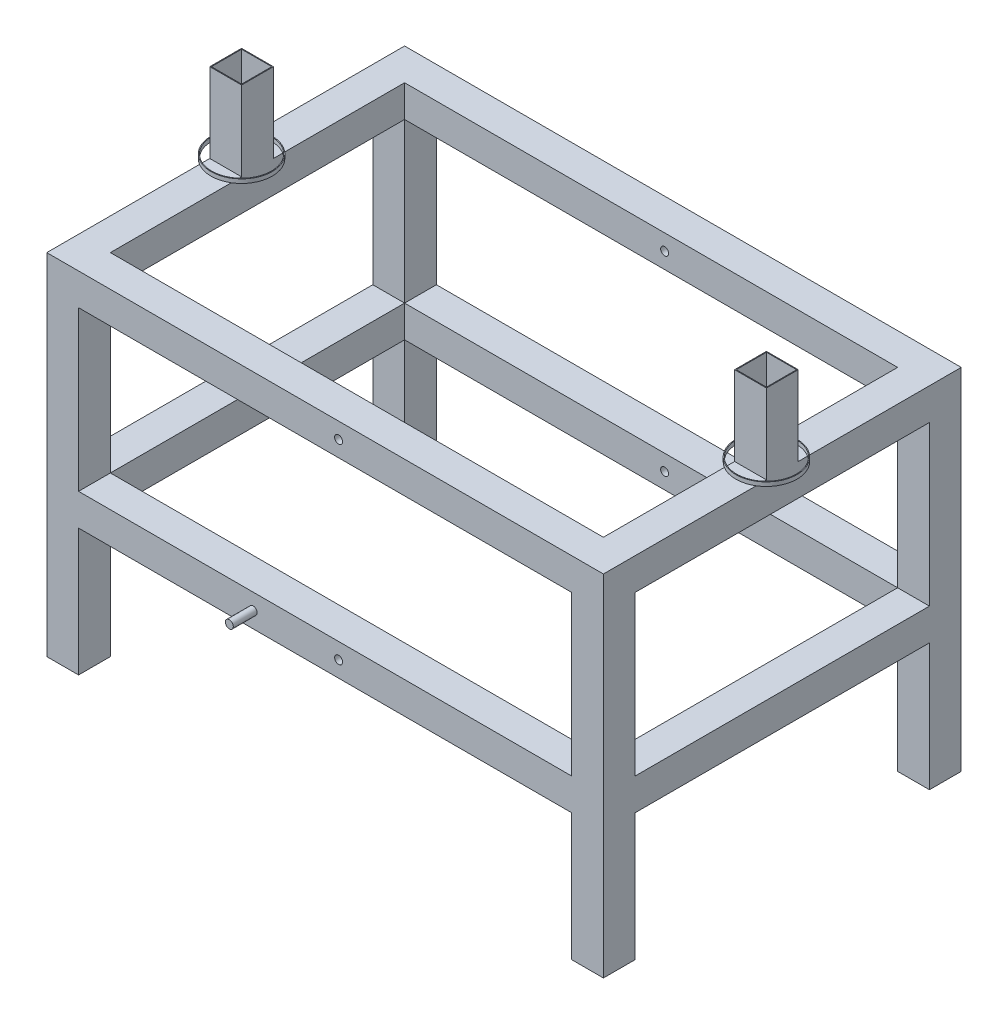
SolidWorks part; units mm, degrees
ref_plane "Front Plane" through (0, 0, 0) normal (0, 0, 1) x (1, 0, 0)
ref_plane "Top Plane" through (0, 0, 0) normal (0, 1, 0) x (1, 0, 0)
ref_plane "Right Plane" through (0, 0, 0) normal (1, 0, 0) x (0, 0, -1)
sketch "Sketch1" plane through (0, 0, 0) normal (0, 1, 0) x (1, 0, 0)
  line L0 (-349, 186) -> (-311, 186)
  line L1 (-350, 225) -> (350, 225) construction
  line L2 (-350, 225) -> (-350, -225) construction
  line L3 (-350, -225) -> (350, -225) construction
  line L4 (350, 225) -> (350, -225) construction
  line L5 (-350, 225) -> (350, -225) construction
  line L6 (-350, -225) -> (350, 225) construction
  line L7 (-350, 225) -> (-310, 225)
  line L8 (-350, 225) -> (-350, 185)
  line L9 (-350, 185) -> (-310, 185)
  line L10 (-310, 225) -> (-310, 185)
  line L11 (350, 225) -> (310, 225)
  line L12 (350, 225) -> (350, 185)
  line L13 (350, 185) -> (310, 185)
  line L14 (310, 225) -> (310, 185)
  line L15 (350, -225) -> (310, -225)
  line L16 (350, -225) -> (350, -185)
  line L17 (350, -185) -> (310, -185)
  line L18 (310, -225) -> (310, -185)
  line L19 (-350, -225) -> (-310, -225)
  line L20 (-350, -225) -> (-350, -185)
  line L21 (-350, -185) -> (-310, -185)
  line L22 (-310, -225) -> (-310, -185)
  line L23 (-311, 224) -> (-311, 186)
  line L24 (-349, 224) -> (-311, 224)
  line L25 (-349, 224) -> (-349, 186)
  line L26 (-349, -186) -> (-311, -186)
  line L27 (-311, -224) -> (-311, -186)
  line L28 (-349, -224) -> (-311, -224)
  line L29 (-349, -224) -> (-349, -186)
  line L30 (349, -186) -> (311, -186)
  line L31 (311, -224) -> (311, -186)
  line L32 (349, -224) -> (311, -224)
  line L33 (349, -224) -> (349, -186)
  line L34 (349, 186) -> (311, 186)
  line L35 (311, 224) -> (311, 186)
  line L36 (349, 224) -> (311, 224)
  line L37 (349, 224) -> (349, 186)
  point P0 (0, 0)
  dimension "D1" = 700
  dimension "D2" = 450
  dimension "D3" = 40
  dimension "D4" = 40
  dimension "D5" = 40
  dimension "D6" = 40
  dimension "D7" = 40
  dimension "D8" = 40
  dimension "D9" = 40
  dimension "D10" = 40
  dimension "D11" = 1
extrude "Boss-Extrude1" add sketch "Sketch1" along normal mid plane 400
sketch "Sketch2" plane through (0, 200, 0) normal (0, 1, 0) x (1, 0, 0)
  line L0 (310, -225) -> (350, -225) construction
  line L1 (-350, 225) -> (350, 225)
  line L2 (-350, 225) -> (-350, -225)
  line L3 (-350, -225) -> (350, -225)
  line L4 (350, 225) -> (350, -225)
  line L5 (-350, 185) -> (-310, 185) construction
  line L6 (310, -185) -> (-310, -185)
  line L7 (310, -185) -> (310, 185)
  line L8 (310, 185) -> (-310, 185)
  line L9 (-310, -185) -> (-310, 185)
extrude "Boss-Extrude2" add sketch "Sketch2" along normal blind 40
sketch "Sketch3" plane through (0, 240, 0) normal (0, 1, 0) x (1, 0, 0)
  line L0 (-350, 0) -> (350, 0) construction
  line L1 (-350, 225) -> (-350, -225) construction
  line L2 (350, -225) -> (350, 225) construction
  line L3 (-310, 185) -> (-310, -185) construction
  line L4 (-350, 20) -> (-310, 20)
  line L5 (-350, 20) -> (-350, -20)
  line L6 (-350, -20) -> (-310, -20)
  line L7 (-310, 20) -> (-310, -20)
  line L8 (310, -185) -> (310, 185) construction
  line L9 (310, -20) -> (350, -20)
  line L10 (310, -20) -> (310, 20)
  line L11 (310, 20) -> (350, 20)
  line L12 (350, -20) -> (350, 20)
  line L13 (311, 19) -> (349, 19)
  line L14 (349, -19) -> (349, 19)
  line L15 (311, -19) -> (349, -19)
  line L16 (311, -19) -> (311, 19)
  line L17 (-349, 19) -> (-311, 19)
  line L18 (-311, 19) -> (-311, -19)
  line L19 (-349, -19) -> (-311, -19)
  line L20 (-349, 19) -> (-349, -19)
  dimension "D1" = 40
  dimension "D2" = 40
  dimension "D3" = 1
  dimension "D4" = 1
extrude "Boss-Extrude4" add sketch "Sketch3" along normal blind 100
sketch "Sketch4" plane through (0, 0, 225) normal (0, 0, 1) x (1, 0, 0)
  line L0 (-350, 240) -> (-350, -200) construction
  line L1 (-310, 200) -> (310, 200) construction
  circle A0 centre (17, 220) radius 5
  dimension "D3" = 10
  dimension "D1" = 367
  dimension "D2" = 20
extrude "Cut-Extrude1" cut sketch "Sketch4" against normal blind 465
sketch "Sketch5" plane through (0, 0, 0) normal (0, 1, 0) x (1, 0, 0)
  line L1 (-350, 225) -> (350, 225)
  line L2 (-350, 225) -> (-350, -225)
  line L3 (-350, -225) -> (350, -225)
  line L4 (350, 225) -> (350, -225)
  line L5 (-310, 185) -> (310, 185)
  line L6 (-310, 185) -> (-310, -185)
  line L7 (-310, -185) -> (310, -185)
  line L8 (310, 185) -> (310, -185)
extrude "Boss-Extrude5" add sketch "Sketch5" against normal blind 40
sketch "Sketch6" plane through (0, 0, 225) normal (0, 0, 1) x (1, 0, 0)
  line L1 (-310, 0) -> (310, 0) construction
  line L2 (-350, 240) -> (-350, -200) construction
  circle A1 centre (17, -20) radius 5
  dimension "D2" = 10
  dimension "D1" = 20
  dimension "D3" = 367
extrude "Cut-Extrude2" cut sketch "Sketch6" against normal blind 508
sketch "Sketch7" plane through (0, 240, 0) normal (0, 1, 0) x (1, 0, 0)
  line L0 (-350, -20) -> (-350, -225) construction
  line L1 (-349, -19) -> (-311, -19) construction
  line L2 (0, 253.038) -> (0, -258.0792) construction
  circle A0 centre (-330, 0) radius 37.5
  circle A1 centre (-330, 0) radius 38.5
  circle A2 centre (330, 0) radius 38.5
  circle A3 centre (330, 0) radius 37.5
  dimension "D1" = 75
  dimension "D2" = 20
  dimension "D3" = 19
  dimension "D4" = 1
extrude "Boss-Extrude6" add sketch "Sketch7" along normal blind 5
sketch "Sketch8" plane through (0, 0, 225) normal (0, 0, 1) x (1, 0, 0)
  line L0 (-310, -40) -> (310, -40) construction
  circle A0 centre (-90.4244, -20) radius 5
  dimension "D1" = 10
  dimension "D2" = 20
extrude "Boss-Extrude7" add sketch "Sketch8" along normal blind 30
